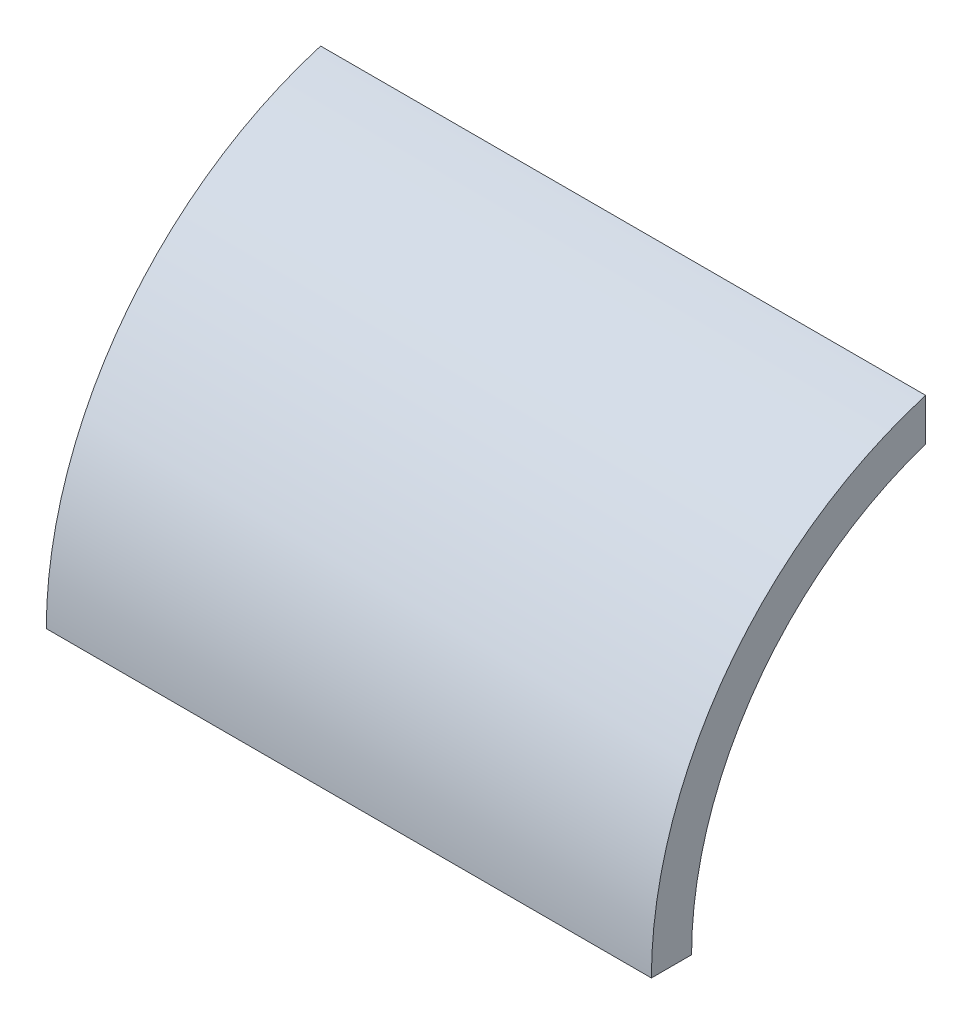
SolidWorks part; units mm, degrees
material "1060 Alloy"
ref_plane "Front" through (0, 0, 0) normal (0, 0, 1) x (1, 0, 0)
ref_plane "Top" through (0, 0, 0) normal (0, 1, 0) x (1, 0, 0)
ref_plane "Right" through (0, 0, 0) normal (1, 0, 0) x (0, 0, -1)
sketch "Sketch1" plane through (0, 0, 0) normal (1, 0, 0) x (0, 0, -1)
  line L0 (-57.6072, 0) -> (-64.3541, 0)
  line L1 (-18.2961, 54.6246) -> (-18.2961, 61.6985)
  line L2 (50, 0) -> (-50, 0) construction
  arc A0 (-18.2961, 54.6246) -> (-57.6072, 0) centre (0, 0) ccw
  arc A1 (-64.3541, 0) -> (-18.2961, 61.6985) centre (0, 0) cw
  dimension "D1" = 57.6072
  dimension "D2" = 6.7469
  dimension "D3" = 76.9938
extrude "Boss-Extrude1" add sketch "Sketch1" along normal blind 101.6
equation "\"Total Cutting Length\"= \"Cutting Length-Outer\" + \"Cutting Length-Inner\""
equation "\"Amount in ft^2\"= \"Bounding Box Area-Blank\" / 144"
